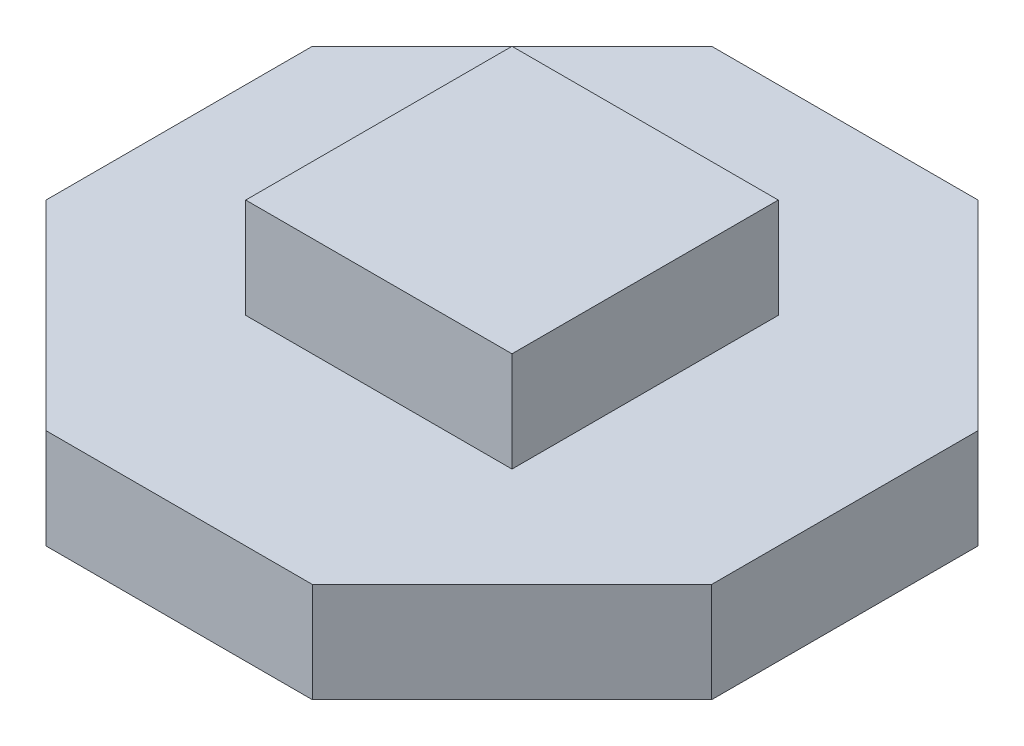
SolidWorks part; units mm, degrees
ref_plane "Front Plane" through (0, 0, 0) normal (0, 0, 1) x (1, 0, 0)
ref_plane "Top Plane" through (0, 0, 0) normal (0, 1, 0) x (1, 0, 0)
ref_plane "Right Plane" through (0, 0, 0) normal (1, 0, 0) x (0, 0, -1)
sketch "Sketch1" plane through (0, 0, 0) normal (0, 1, 0) x (1, 0, 0)
  line L0 (0, 7.8311) -> (0, -11.2785) construction
  line L1 (-5, 5) -> (5, 5)
  line L2 (-5, 5) -> (-5, -5)
  line L3 (-5, -5) -> (5, -5)
  line L4 (5, 5) -> (5, -5)
  line L5 (-12.0776, 0) -> (13.0365, 0) construction
  dimension "D1" = 10
  dimension "D2" = 10
extrude "Boss-Extrude1" add sketch "Sketch1" along normal blind 1.5
sketch "Sketch2" plane through (0, 1.5, 0) normal (0, 1, 0) x (1, 0, 0)
  line L0 (0, -5.5183) -> (0, 5.397) construction
  line L1 (-2, 2) -> (2, 2)
  line L2 (-2, 2) -> (-2, -2)
  line L3 (-2, -2) -> (2, -2)
  line L4 (2, 2) -> (2, -2)
  line L5 (-5.5703, 0) -> (6.7744, 0) construction
  dimension "D1" = 4
  dimension "D2" = 4
extrude "Boss-Extrude2" add sketch "Sketch2" along normal blind 1.5
sketch "Sketch3" plane through (0, 1.5, 0) normal (0, 1, 0) x (1, 0, 0)
  line L0 (-5, 2) -> (-2, 5)
  line L1 (-5, 5) -> (-5, -5) construction
  line L2 (5, 5) -> (-5, 5) construction
  line L3 (-5, 2) -> (-5, 5)
  line L4 (-5, 5) -> (-2, 5)
  dimension "D1" = 3
  dimension "D2" = 3
extrude "Cut-Extrude1" cut sketch "Sketch3" against normal up to next (1.5 mm away)
sketch "Sketch4" plane through (0, 3, 0) normal (0, 1, 0) x (1, 0, 0)
  circle A0 centre (0, 0) radius 1.0659 construction
pattern_circular "CirPattern1" count 4 over 360 about axis through (0, 0, 0) along (0, 1, 0) of "Cut-Extrude1"
